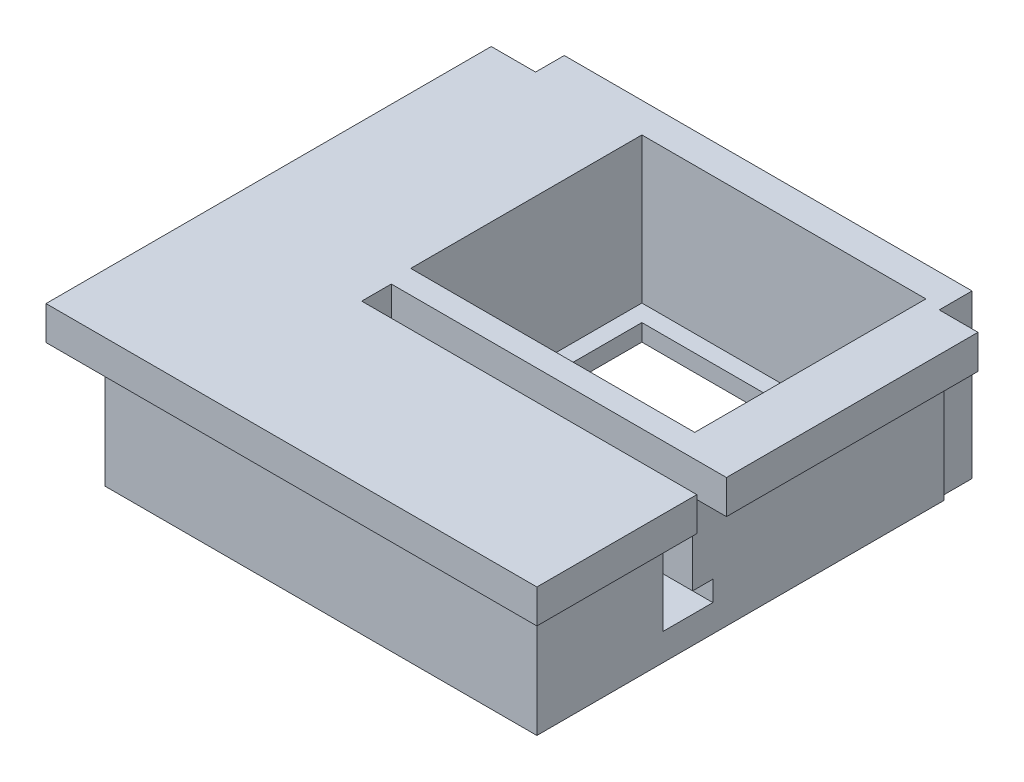
SolidWorks part; units mm, degrees
ref_plane "Front Plane" through (0, 0, 0) normal (0, 0, 1) x (1, 0, 0)
ref_plane "Top Plane" through (0, 0, 0) normal (0, 1, 0) x (1, 0, 0)
ref_plane "Right Plane" through (0, 0, 0) normal (1, 0, 0) x (0, 0, -1)
sketch "Sketch4" plane through (-9.897, 0, -25.5164) normal (0, 1, 0) x (1, 0, 0)
  line L1 (-26.0867, 10.5277) -> (-0.5867, 10.5277)
  line L2 (-26.0867, 10.5277) -> (-26.0867, -15.4723)
  line L3 (-26.0867, -15.4723) -> (-0.5867, -15.4723)
  line L4 (-0.5867, 10.5277) -> (-0.5867, -15.4723)
extrude "Boss-Extrude6" add sketch "Sketch4" along normal blind 9.6 separate body contours L1 L4 L3 L2
sketch "Sketch17" plane through (-9.897, 9.6, -25.5164) normal (0, 1, 0) x (1, 0, 0)
  line L1 (-26.0867, 10.5277) -> (-24.9695, 10.5277)
  line L2 (-26.0867, 10.5277) -> (-26.0867, 8.8322)
  line L3 (-26.0867, 8.8322) -> (-24.9695, 8.8322)
  line L4 (-24.9695, 10.5277) -> (-24.9695, 8.8322)
extrude "Cut-Extrude3" cut sketch "Sketch17" against normal blind 9.6
sketch "Sketch18" plane through (-9.897, 9.6, -25.5164) normal (0, 1, 0) x (1, 0, 0)
  line L0 (-0.5867, 10.5277) -> (-0.5867, -15.4723) construction
  line L1 (-0.5867, -6.2725) -> (-18.3871, -6.2725)
  line L2 (-0.5867, -6.2725) -> (-0.5867, -8.0225)
  line L3 (-0.5867, -8.0225) -> (-18.3871, -8.0225)
  line L4 (-18.3871, -6.2725) -> (-18.3871, -8.0225)
extrude "Cut-Extrude10" cut sketch "Sketch18" against normal blind 8
sketch "Sketch19" plane through (-10.4837, 0, 0) normal (1, 0, 0) x (0, 0, -1)
  line L1 (19.2439, 1.6) -> (20.4439, 1.6)
  line L2 (19.2439, 1.6) -> (19.2439, 2.8)
  line L5 (19.2439, 2.8) -> (20.4439, 2.8)
  line L6 (20.4439, 1.6) -> (20.4439, 2.8)
sketch "Sketch20" plane through (0, 9.6, -0.0788) normal (0, 1, 0) x (1, 0, 0)
  line L1 (-11.7307, 34.194) -> (-28.5094, 34.194)
  line L2 (-11.7307, 34.194) -> (-11.7307, 20.5364)
  line L3 (-11.7307, 20.5364) -> (-28.5094, 20.5364)
  line L4 (-28.5094, 34.194) -> (-28.5094, 20.5364)
extrude "Cut-Extrude13" cut sketch "Sketch20" against normal blind 10.5
sketch "Sketch21" plane through (0, 9.6, 0) normal (0, 1, 0) x (1, 0, 0)
  line L1 (-10.4837, 36.0442) -> (-10.7751, 36.0442)
  line L2 (-10.4837, 36.0442) -> (-10.4837, 34.1041)
  line L3 (-10.4837, 34.1041) -> (-10.7751, 34.1041)
  line L4 (-10.7751, 36.0442) -> (-10.7751, 34.1041)
extrude "Cut-Extrude14" cut sketch "Sketch21" against normal blind 10.5
sketch "Sketch22" plane through (-10.4837, 0, 0) normal (1, 0, 0) x (0, 0, -1)
  line L0 (19.2439, 1.6) -> (19.2439, 9.6) construction
  line L1 (34.1041, 9.6) -> (19.2439, 9.6)
  line L2 (34.1041, 9.6) -> (34.1041, 7.5976)
  line L3 (34.1041, 7.5976) -> (19.2439, 7.5976)
  line L4 (19.2439, 9.6) -> (19.2439, 7.5976)
extrude "Boss-Extrude7" add sketch "Sketch22" along normal blind 2
sketch "Sketch23" plane through (-10.4837, 0, 0) normal (1, 0, 0) x (0, 0, -1)
  line L0 (10.0442, 9.6) -> (10.0442, 0) construction
  line L1 (17.4939, 9.6) -> (10.0442, 9.6)
  line L2 (17.4939, 9.6) -> (17.4939, 7.605)
  line L3 (17.4939, 7.605) -> (10.0442, 7.605)
  line L4 (10.0442, 9.6) -> (10.0442, 7.605)
extrude "Boss-Extrude8" add sketch "Sketch23" along normal blind 2
sketch "Sketch24" plane through (0, 0, -10.0442) normal (0, 0, 1) x (1, 0, 0)
  line L1 (-35.9837, 9.6) -> (-8.4837, 9.6)
  line L2 (-35.9837, 9.6) -> (-35.9837, 7.605)
  line L3 (-35.9837, 7.605) -> (-8.4837, 7.605)
  line L4 (-8.4837, 9.6) -> (-8.4837, 7.605)
extrude "Boss-Extrude9" add sketch "Sketch24" along normal blind 2
sketch "Sketch25" plane through (-35.9837, 0, 0) normal (-1, 0, 0) x (0, 0, 1)
  line L1 (-34.3486, 9.6) -> (-8.0442, 9.6)
  line L2 (-34.3486, 9.6) -> (-34.3486, 7.605)
  line L3 (-34.3486, 7.605) -> (-8.0442, 7.605)
  line L4 (-8.0442, 9.6) -> (-8.0442, 7.605)
extrude "Boss-Extrude10" add sketch "Sketch25" along normal blind 1.5
extrude "Cut-Extrude15" cut sketch "Sketch19" against normal blind 18.5 and the other way through all
sketch "Sketch26" plane through (-28.5094, 0, -0.0788) normal (1, 0, 0) x (0, 0, -1)
  line L0 (34.194, 0) -> (34.194, 9.6) construction
  line L1 (20.5364, 0) -> (34.194, 0)
  line L2 (20.5364, 0) -> (20.5364, 1)
  line L3 (20.5364, 1) -> (34.194, 1)
  line L4 (34.194, 0) -> (34.194, 1)
extrude "Boss-Extrude11" add sketch "Sketch26" along normal blind 1
sketch "Sketch27" plane through (0, 0, -34.2728) normal (0, 0, 1) x (1, 0, 0)
  line L1 (-11.7307, 0) -> (-27.5094, 0)
  line L2 (-11.7307, 0) -> (-11.7307, 1)
  line L3 (-11.7307, 1) -> (-27.5094, 1)
  line L4 (-27.5094, 0) -> (-27.5094, 1)
extrude "Boss-Extrude12" add sketch "Sketch27" along normal blind 1
sketch "Sketch28" plane through (-11.7307, 0, -0.0788) normal (-1, 0, 0) x (0, 0, 1)
  line L0 (-20.5364, 0) -> (-20.5364, 9.6) construction
  line L1 (-33.194, 0) -> (-20.5364, 0)
  line L2 (-33.194, 0) -> (-33.194, 1)
  line L3 (-33.194, 1) -> (-20.5364, 1)
  line L4 (-20.5364, 0) -> (-20.5364, 1)
extrude "Boss-Extrude13" add sketch "Sketch28" along normal blind 1
sketch "Sketch29" plane through (0, 0, -20.6152) normal (0, 0, -1) x (-1, 0, 0)
  line L1 (12.7307, 0) -> (27.5094, 0)
  line L2 (12.7307, 0) -> (12.7307, 1)
  line L3 (12.7307, 1) -> (27.5094, 1)
  line L4 (27.5094, 0) -> (27.5094, 1)
extrude "Boss-Extrude14" add sketch "Sketch29" along normal blind 1
